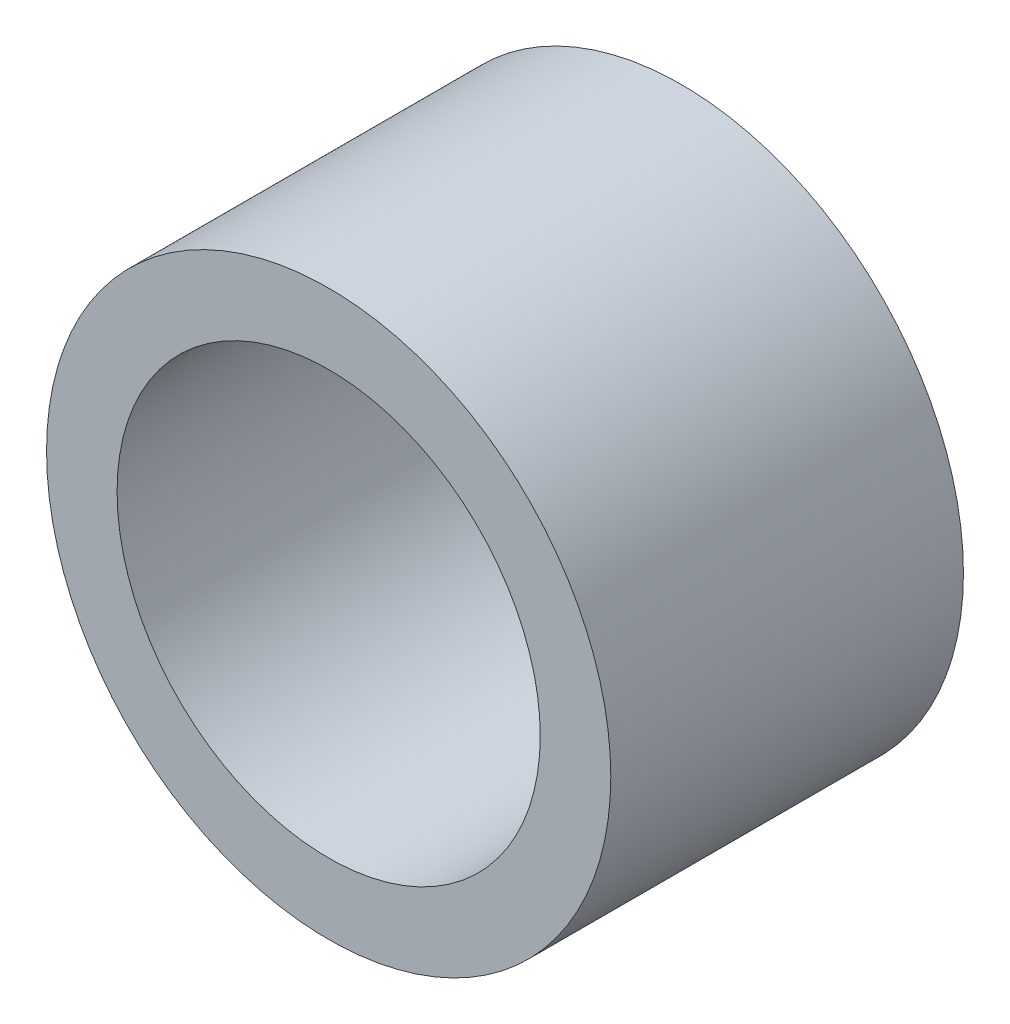
SolidWorks part; units mm, degrees
ref_plane "前视基准面" through (0, 0, 0) normal (0, 0, 1) x (1, 0, 0)
ref_plane "上视基准面" through (0, 0, 0) normal (0, 1, 0) x (1, 0, 0)
ref_plane "右视基准面" through (0, 0, 0) normal (1, 0, 0) x (0, 0, -1)
sketch "草图1" plane through (0, 0, 0) normal (0, 0, 1) x (1, 0, 0)
  circle A0 centre (0, 0) radius 4
  circle A1 centre (0, 0) radius 3
  dimension "D1" = 8
  dimension "D2" = 6
extrude "凸台-拉伸1" add sketch "草图1" along normal blind 5
